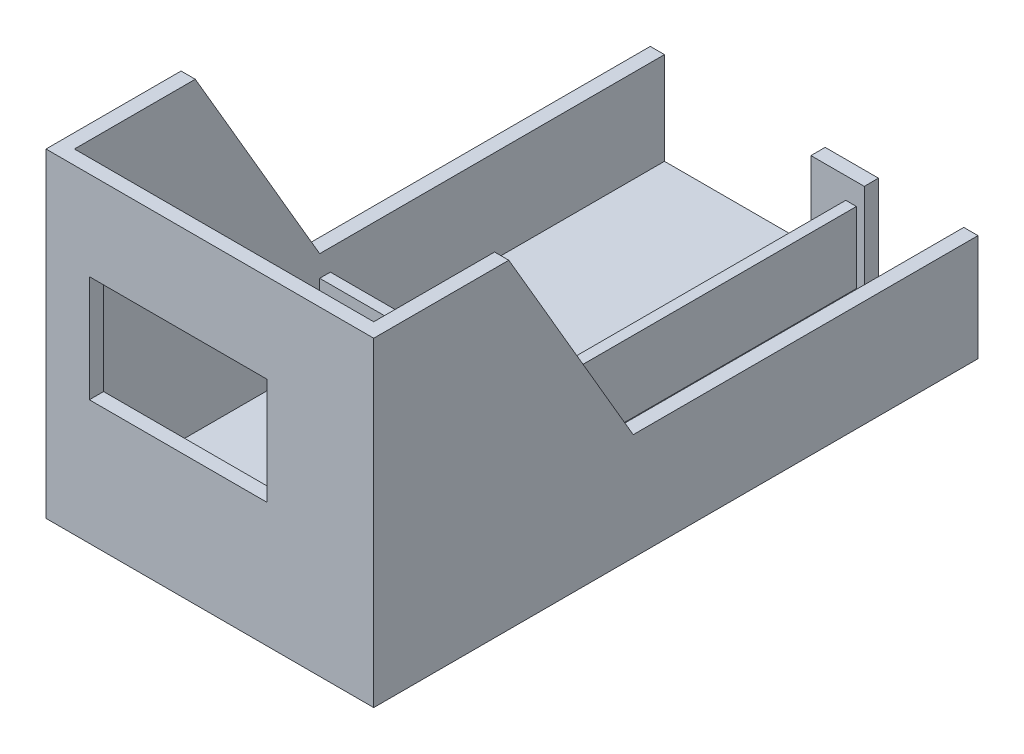
SolidWorks part; units mm, degrees
ref_plane "Front Plane" through (0, 0, 0) normal (0, 0, 1) x (1, 0, 0)
ref_plane "Top Plane" through (0, 0, 0) normal (0, 1, 0) x (1, 0, 0)
ref_plane "Right Plane" through (0, 0, 0) normal (1, 0, 0) x (0, 0, -1)
sketch "Sketch1" plane through (0, 0, 0) normal (0, 1, 0) x (1, 0, 0)
  line L1 (-46.1, 85) -> (46.1, 85)
  line L2 (-46.1, 85) -> (-46.1, -85)
  line L3 (-46.1, -85) -> (46.1, -85)
  line L4 (46.1, 85) -> (46.1, -85)
  line L5 (-46.1, 85) -> (46.1, -85) construction
  line L6 (-46.1, -85) -> (46.1, 85) construction
  point P0 (0, 0)
  dimension "D1" = 170
  dimension "D2" = 92.2
extrude "Box" add sketch "Sketch1" along normal blind 90
sketch "Sketch2" plane through (0, 90, 0) normal (0, 1, 0) x (1, 0, 0)
  line L0 (46.1, 85) -> (-46.1, 85) construction
  line L1 (-42.1, 81) -> (42.1, 81)
  line L2 (-42.1, 81) -> (-42.1, -81)
  line L3 (-42.1, -81) -> (42.1, -81)
  line L4 (42.1, 81) -> (42.1, -81)
  line L5 (-42.1, 81) -> (42.1, -81) construction
  line L6 (-42.1, -81) -> (42.1, 81) construction
  line L7 (46.1, -85) -> (46.1, 85) construction
  point P0 (0, 0)
  dimension "D1" = 4
  dimension "D2" = 4
extrude "Box Cut" cut sketch "Sketch2" against normal blind 86
sketch "Inside Walls" plane through (0, 4, 0) normal (0, 1, 0) x (1, 0, 0)
  line L0 (42.1, -81) -> (42.1, 81) construction
  line L1 (-42.1, -81) -> (16.1, -81) construction
  line L2 (-42.1, -81) -> (-42.1, -12) construction
  line L3 (-42.1, -12) -> (16.1, -12) construction
  line L4 (16.1, -81) -> (16.1, -12) construction
  line L5 (-42.1, -9) -> (12.9, -9) construction
  line L6 (-42.1, -9) -> (-42.1, 67) construction
  line L7 (-42.1, 67) -> (12.9, 67) construction
  line L8 (12.9, -9) -> (12.9, 67) construction
  line L10 (-42.1, -12) -> (19.1, -12)
  line L11 (-42.1, -12) -> (-42.1, -9)
  line L12 (-42.1, -9) -> (19.1, -9)
  line L13 (19.1, -12) -> (19.1, -9)
  line L14 (16.1, -81) -> (19.1, -81)
  line L15 (16.1, -81) -> (16.1, -12)
  line L16 (16.1, -12) -> (19.1, -12)
  line L17 (19.1, -81) -> (19.1, -12)
  line L18 (12.9, -9) -> (15.9, -9)
  line L19 (12.9, -9) -> (12.9, 81)
  line L20 (12.9, 81) -> (15.9, 81)
  line L21 (15.9, -9) -> (15.9, 81)
  line L25 (12.9, 67) -> (12.9, 69.994)
  line L26 (19.1, 86) -> (42.1, 86) construction
  line L27 (19.1, 86) -> (19.1, -81) construction
  line L28 (19.1, -81) -> (42.1, -81) construction
  line L29 (42.1, 86) -> (42.1, -81) construction
  line L31 (42.1, 81) -> (-42.1, 81) construction
  point P26 (96.4126, -80.2808)
  point P27 (46, -81)
  dimension "D1" = 69
  dimension "D2" = 58.2
  dimension "D3" = 55
  dimension "D4" = 76
  dimension "D5" = 26
  dimension "D6" = 3
  dimension "D7" = 3
  dimension "D8" = 0
  dimension "D9" = 3
  dimension "D10" = 23
  dimension "D11" = 167
extrude "Boss-Extrude2" add sketch "Inside Walls" along normal blind 20
sketch "Sketch4" plane through (0, 0, -85) normal (0, 0, -1) x (-1, 0, 0)
  line L1 (-42.1, 4) -> (-18.1, 4)
  line L2 (-42.1, 4) -> (-42.1, 86)
  line L3 (-42.1, 86) -> (-18.1, 86)
  line L4 (-18.1, 4) -> (-18.1, 86)
  line L5 (-46.1, 90) -> (-46.1, 0) construction
  line L6 (46.1, 0) -> (-46.1, 0) construction
  line L7 (46.1, 0) -> (-46.1, 0) construction
  line L8 (42.1, 4) -> (-3.1, 4)
  line L9 (42.1, 4) -> (42.1, 34)
  line L10 (42.1, 34) -> (-3.1, 34)
  line L11 (-3.1, 4) -> (-3.1, 34)
  line L12 (46.1, 90) -> (46.1, 0) construction
  dimension "D1" = 82
  dimension "D2" = 4
  dimension "D3" = 24
  dimension "D4" = 4
  dimension "D5" = 4
  dimension "D6" = 4
  dimension "D7" = 15
  dimension "D8" = 30
extrude "Cut-Extrude2" cut sketch "Sketch4" against normal blind 4
sketch "Sketch5" plane through (-46.1, 0, 0) normal (-1, 0, 0) x (0, 0, 1)
  line L0 (-85, 90) -> (-85, 0) construction
  line L1 (-69.9955, 60) -> (-29.9955, 60)
  line L2 (-69.9955, 60) -> (-69.9955, 40)
  line L3 (-69.9955, 40) -> (-29.9955, 40)
  line L4 (-29.9955, 60) -> (-29.9955, 40)
  line L5 (-85, 90) -> (85, 90) construction
  point P6 (-85, 45)
  dimension "D1" = 15.0045
  dimension "D2" = 30
  dimension "D3" = 20
  dimension "D4" = 40
extrude "Cut-Extrude3" cut sketch "Sketch5" against normal blind 104
sketch "Sketch6" plane through (0, 0, 85) normal (0, 0, 1) x (1, 0, 0)
  line L0 (46.1, 90) -> (46.1, 0) construction
  line L5 (-46.1, 90) -> (46.1, 90) construction
  line L6 (0, 90) -> (0, 0) construction
  line L8 (-33.9, 65) -> (16.1, 65)
  line L9 (-33.9, 65) -> (-33.9, 35)
  line L10 (-33.9, 35) -> (16.1, 35)
  line L11 (16.1, 65) -> (16.1, 35)
  line L12 (-33.9, 65) -> (16.1, 35) construction
  line L13 (-33.9, 35) -> (16.1, 65) construction
  dimension "D1" = 30
  dimension "D2" = 50
  dimension "D3" = 25
  dimension "D4" = 30
extrude "Cut-Extrude4" cut sketch "Sketch6" against normal blind 14
sketch "Sketch7" plane through (0, 90, 0) normal (0, 1, 0) x (1, 0, 0)
  line L1 (-46.1, -12) -> (46.1, -12)
  line L2 (-46.1, -12) -> (-46.1, 85)
  line L3 (-46.1, 85) -> (46.1, 85)
  line L4 (46.1, -12) -> (46.1, 85)
  line L5 (-42.1, -12) -> (16.1, -12) construction
  line L6 (-46.1, 85) -> (46.1, 85) construction
  point P6 (0, 0)
  point P7 (0, 0)
  dimension "D1" = 0
  dimension "D2" = 0
extrude "Cut-Extrude5" cut sketch "Sketch7" against normal blind 60
sketch "Sketch8" plane through (46.1, 0, 0) normal (1, 0, 0) x (0, 0, -1)
  line L0 (-12, 30) -> (-47, 90)
  line L1 (-85, 90) -> (-12, 90) construction
  line L2 (-47, 90) -> (-12, 90)
  line L3 (-12, 90) -> (-12, 30)
  dimension "D1" = 35
extrude "Cut-Extrude6" cut sketch "Sketch8" against normal blind 100
